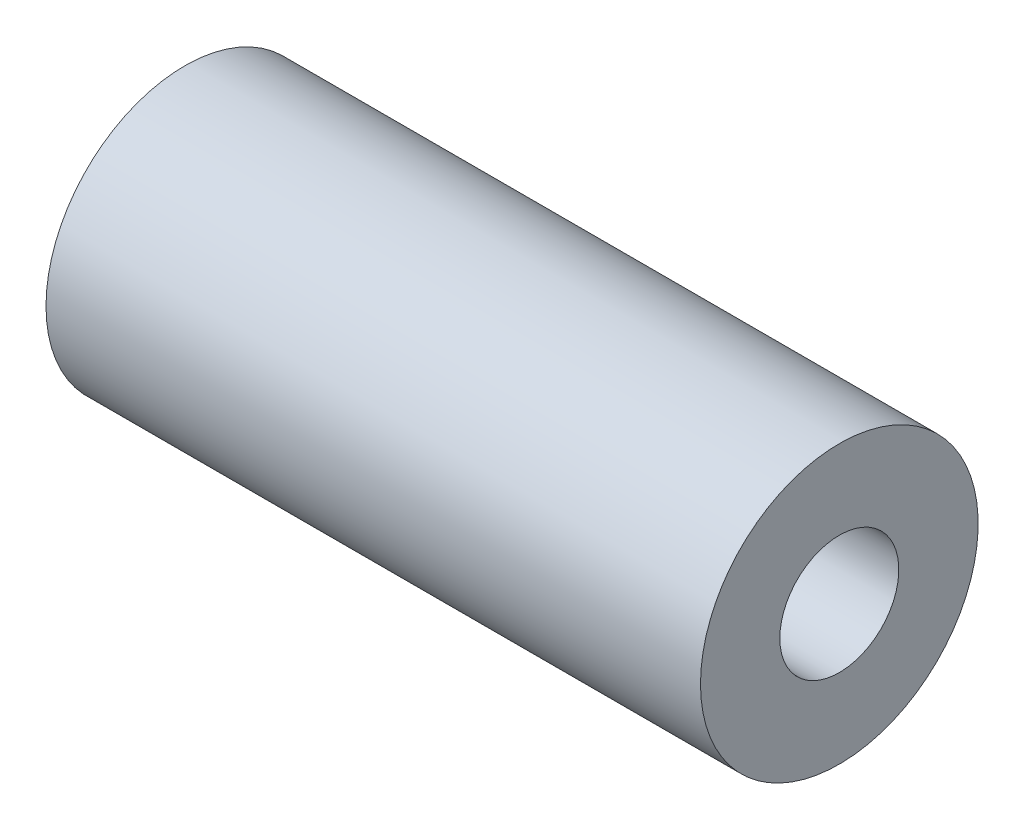
SolidWorks part; units mm, degrees
material "POM Acetal Copolymer"
ref_plane "Front Plane" through (0, 0, 0) normal (0, 0, 1) x (1, 0, 0)
ref_plane "Top Plane" through (0, 0, 0) normal (0, 1, 0) x (1, 0, 0)
ref_plane "Right Plane" through (0, 0, 0) normal (1, 0, 0) x (0, 0, -1)
sketch "Sketch1" plane through (0, 0, 0) normal (0, 0, 1) x (1, 0, 0)
  line L0 (-37.0032, 0) -> (16.5, 0) construction
  line L1 (-16.5, 7) -> (16.5, 7)
  line L2 (-16.5, 7) -> (-16.5, 3)
  line L3 (-16.5, 3) -> (16.5, 3)
  line L4 (16.5, 7) -> (16.5, 3)
  line L5 (16.5, 0) -> (16.5, 3) construction
  line L6 (0, 0) -> (0, 7) construction
  dimension "D1" = 6
  dimension "D2" = 33
  dimension "D3" = 14
revolve "Revolve1" add sketch "Sketch1" angle 360 about L0
